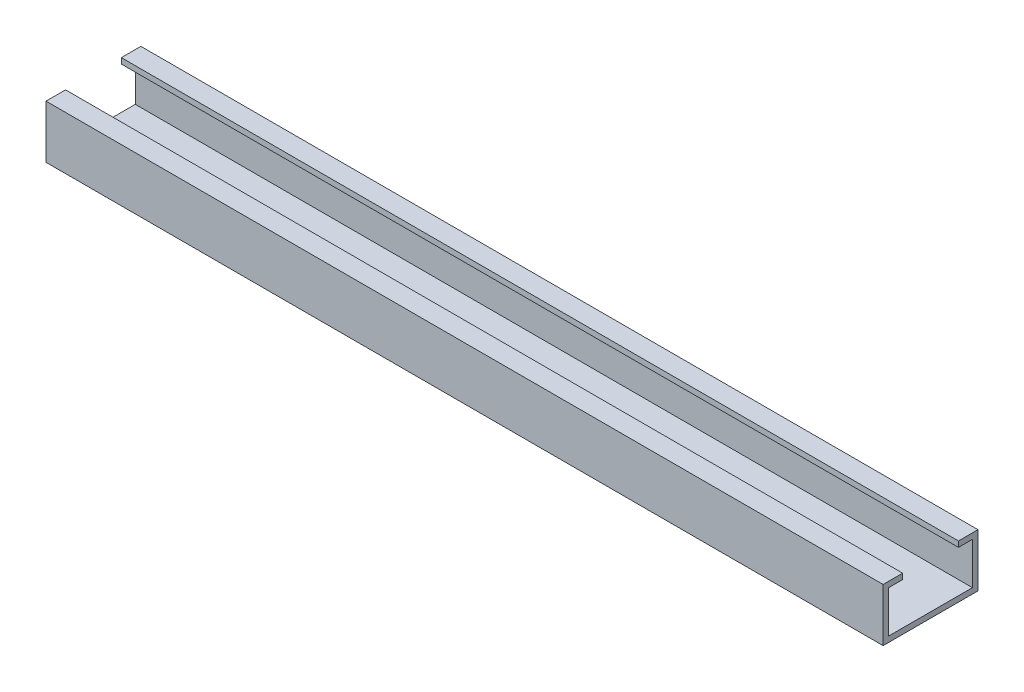
SolidWorks part; units mm, degrees
ref_plane "Спереди" through (0, 0, 0) normal (0, 0, 1) x (1, 0, 0)
ref_plane "Сверху" through (0, 0, 0) normal (0, 1, 0) x (1, 0, 0)
ref_plane "Справа" through (0, 0, 0) normal (1, 0, 0) x (0, 0, -1)
sketch "Эскиз1" plane through (0, 0, 0) normal (1, 0, 0) x (0, 0, -1)
  line L0 (-15, 0) -> (15, 0)
  line L1 (15, 0) -> (15, 15)
  line L2 (15, 15) -> (10, 15)
  line L3 (-15, 0) -> (-15, 15)
  line L4 (-15, 15) -> (-10, 15)
  point P3 (0, 0)
  point P8 (0, 0)
  point P9 (0, 0)
  point P10 (0, 0)
  point P11 (0, 0)
extrude "Вытянуть-Тонкостенный1" add sketch "Эскиз1" along normal blind 300 thin
